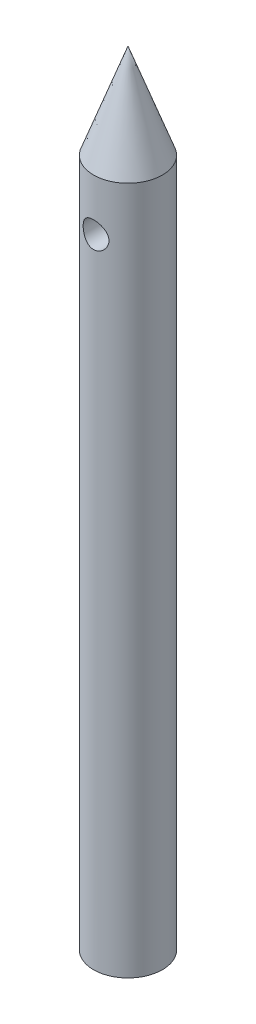
SolidWorks part; units mm, degrees
ref_plane "Front Plane" through (0, 0, 0) normal (0, 0, 1) x (1, 0, 0)
ref_plane "Top Plane" through (0, 0, 0) normal (0, 1, 0) x (1, 0, 0)
ref_plane "Right Plane" through (0, 0, 0) normal (1, 0, 0) x (0, 0, -1)
sketch "Sketch1" plane through (0, 0, 0) normal (0, 1, 0) x (1, 0, 0)
  circle A0 centre (0, 0) radius 2
  dimension "D1" = 4
extrude "Boss-Extrude1" add sketch "Sketch1" along normal blind 40
cosmetic thread "Cosmetic Thread1" parameters "D1"=7, "D2"=2.439
sketch "Sketch7" plane through (0, 40, 0) normal (0, 1, 0) x (1, 0, 0)
  circle A0 centre (0, 0) radius 2 construction
  circle A1 centre (0, 0) radius 2
extrude "Boss-Extrude2" add sketch "Sketch7" along normal blind 7 draft 20 separate body
ref_plane "Plane2" through (0, 40, 0) normal (0, 1, 0) x (1, 0, 0)
hole_wizard "Ø1.5mm Dowel Hole4" positions "3DSketch7" profile "Sketch21" hole size "Ø1.5" standard "ISO" end condition through all
sketch3d "3DSketch7"
  point P0 (0, 37, 2)
  point P10 (0, 0, 0)
  point P11 (0, 0, 0)
  point P12 (0, 0, 0)
  point P13 (0, 0, 0)
  point P14 (0, 0, 0)
  point P15 (0, 0, 0)
  point P16 (0, 0, 0)
  point P17 (0, 0, 0)
  point P18 (0, 0, 0)
  point P19 (0, 0, 0)
  point P20 (0, 0, 0)
  dimension "D1" = 0
  dimension "D2" = 3
sketch "Sketch21" plane through (0, 37, 2) normal (1, 0, 0) x (0, -1, 0)
  line L0 (0, 0) -> (0, 4)
  line L1 (0, 4) -> (0.75, 4)
  line L2 (0.75, 4) -> (0.75, 0)
  line L5 (0.75, 0) -> (0, 0)
  line L11 (0, -6.35) -> (0, 107.95) construction
  dimension "Thru Hole Dia." = 1.5
  dimension "Thru Hole Depth" = 4
